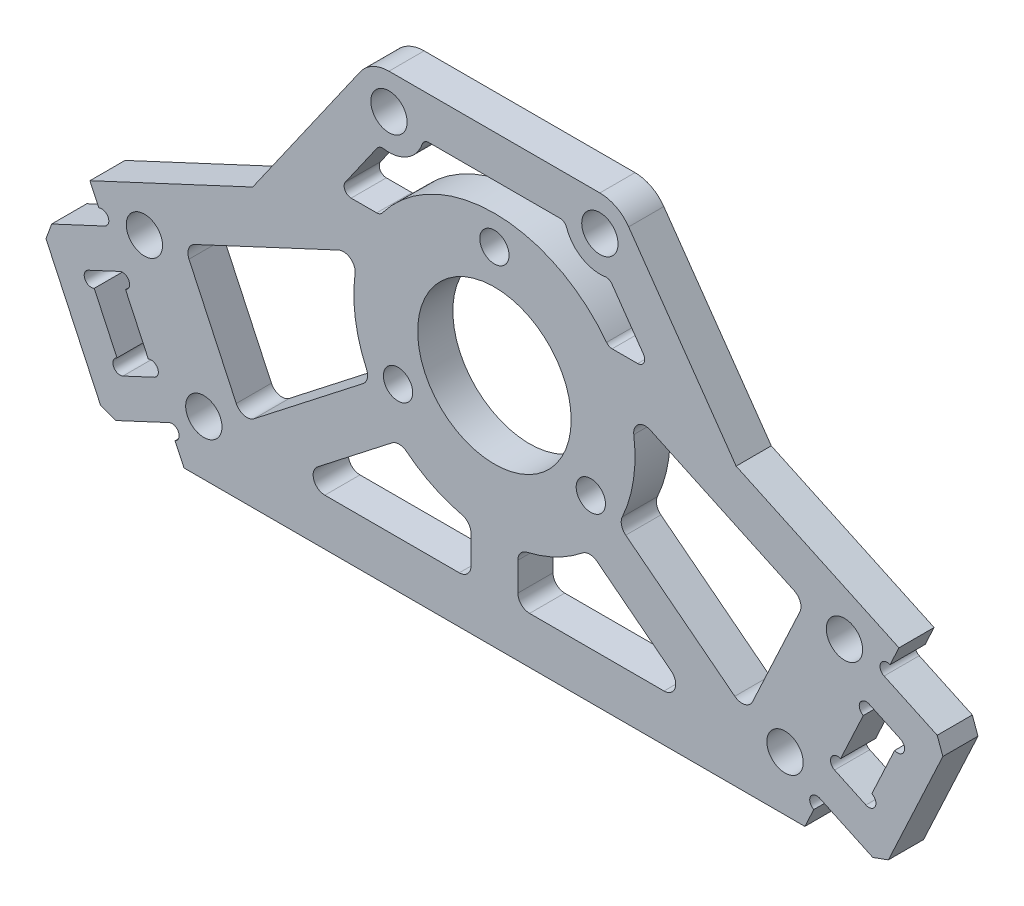
SolidWorks part; units mm, degrees
ref_plane "前视基准面" through (0, 0, 0) normal (0, 0, 1) x (1, 0, 0)
ref_plane "上视基准面" through (0, 0, 0) normal (0, 1, 0) x (1, 0, 0)
ref_plane "右视基准面" through (0, 0, 0) normal (1, 0, 0) x (0, 0, -1)
sketch "草图1" plane through (0, 0, 0) normal (0, 0, 1) x (1, 0, 0)
  line L0 (-34.5264, 8.6099) -> (-26.4967, -8.6099)
  line L1 (-29.455, -2.2658) -> (0, 11.4693) construction
  line L2 (0, -8.6099) -> (0, 8.6099) construction
  line L3 (-34.5264, 8.6099) -> (-5.0714, 22.345)
  line L4 (-26.4967, -8.6099) -> (26.4967, -8.6099)
  line L5 (34.5264, 8.6099) -> (26.4967, -8.6099)
  line L6 (34.5264, 8.6099) -> (5.0714, 22.345)
  circle A0 centre (0, 11.4693) radius 9.5 construction
  circle A1 centre (0, 20.9693) radius 1.25
  circle A2 centre (8.2272, 6.7193) radius 1.25
  circle A3 centre (-8.2272, 6.7193) radius 1.25
  arc A4 (5.0714, 22.345) -> (-5.0714, 22.345) centre (0, 11.4693) ccw
  circle A5 centre (0, 11.4693) radius 6.55
  point P8 (0, 0)
  point P21 (-30.5115, 0)
  dimension "D4" = 19
  dimension "D5" = 2.5
  dimension "D8" = 24
  dimension "D9" = 13.1
  dimension "D1" = 32.5
  dimension "D2" = 25
  dimension "D3" = 19
  dimension "D7" = 2.5
  dimension "D6" = 3
extrude "凸台-拉伸1" add sketch "草图1" along normal mid plane 3
sketch "草图2" plane through (0, 0, 1.5) normal (0, 0, 1) x (1, 0, 0)
  line L0 (-33.2586, 5.891) -> (-38.6964, 3.3553)
  line L1 (-34.5264, 8.6099) -> (-26.4967, -8.6099) construction
  line L2 (-38.6964, 3.3553) -> (-33.2024, -8.4267)
  line L3 (-33.2024, -8.4267) -> (-27.7645, -5.891)
  line L4 (-27.7645, -5.891) -> (-29.0324, -3.1721)
  line L5 (-31.9907, 3.1721) -> (-34.6643, 1.9254)
  line L6 (-34.6643, 1.9254) -> (-31.706, -4.4188)
  line L7 (-31.706, -4.4188) -> (-29.0324, -3.1721)
  line L8 (-31.9907, 3.1721) -> (-33.2586, 5.891)
  line L9 (-30.5115, 0) -> (-33.1852, -1.2467) construction
  line L10 (0, 11.4693) -> (0, -8.6099) construction
  line L11 (-26.4967, -8.6099) -> (26.4967, -8.6099) construction
  line L12 (38.6964, 3.3553) -> (33.2024, -8.4267)
  line L13 (33.2586, 5.891) -> (38.6964, 3.3553)
  line L14 (31.9907, 3.1721) -> (33.2586, 5.891)
  line L15 (31.9907, 3.1721) -> (34.6643, 1.9254)
  line L16 (34.6643, 1.9254) -> (31.706, -4.4188)
  line L17 (31.706, -4.4188) -> (29.0324, -3.1721)
  line L18 (27.7645, -5.891) -> (29.0324, -3.1721)
  line L19 (33.2024, -8.4267) -> (27.7645, -5.891)
  dimension "D1" = 13
  dimension "D2" = 6
  dimension "D3" = 2.95
  dimension "D4" = 7
extrude "凸台-拉伸2" add sketch "草图2" against normal blind 3
sketch "草图3" plane through (0, 0, 1.5) normal (0, 0, 1) x (1, 0, 0)
  line L0 (-34.5264, 8.6099) -> (-33.2586, 5.891) construction
  line L1 (-31.706, -4.4188) -> (-34.6643, 1.9254) construction
  line L3 (-31.9907, 3.1721) -> (-29.0324, -3.1721) construction
  line L4 (-27.7645, -5.891) -> (-26.4967, -8.6099) construction
  line L5 (0, 23.4693) -> (0, -8.6099) construction
  line L6 (-26.4967, -8.6099) -> (26.4967, -8.6099) construction
  circle A0 centre (-33.5121, 6.4348) radius 0.6
  circle A1 centre (-34.4107, 1.3816) radius 0.6
  circle A2 centre (-31.9596, -3.875) radius 0.6
  circle A4 centre (-29.286, -2.6283) radius 0.6
  circle A5 centre (-31.7371, 2.6283) radius 0.6
  circle A6 centre (-27.511, -6.4348) radius 0.6
  arc A7 (5.0714, 22.345) -> (-5.0714, 22.345) centre (0, 11.4693) ccw construction
  circle A8 centre (27.511, -6.4348) radius 0.6
  circle A9 centre (31.7371, 2.6283) radius 0.6
  circle A10 centre (29.286, -2.6283) radius 0.6
  circle A11 centre (31.9596, -3.875) radius 0.6
  circle A12 centre (34.4107, 1.3816) radius 0.6
  circle A13 centre (33.5121, 6.4348) radius 0.6
  dimension "D1" = 1.2
extrude "切除-拉伸1" cut sketch "草图3" against normal through all
sketch "草图4" plane through (0, 0, 1.5) normal (0, 0, 1) x (1, 0, 0)
  line L1 (-5.0714, 22.345) -> (-34.5264, 8.6099) construction
  line L2 (-34.5264, 8.6099) -> (-33.7657, 6.9786) construction
  line L3 (-33.1852, -1.2467) -> (-30.5115, 0) construction
  line L4 (-32.2131, -3.3312) -> (-34.1572, 0.8378) construction
  line L5 (-31.4836, 2.0845) -> (-29.5395, -2.0845) construction
  line L6 (0, 18.0193) -> (0, 4.9193) construction
  circle A0 centre (-29.8752, 6.917) radius 1.55
  circle A4 centre (-24.8038, -3.9587) radius 1.55
  circle A5 centre (0, 11.4693) radius 6.55 construction
  circle A6 centre (24.8038, -3.9587) radius 1.55
  circle A7 centre (29.8752, 6.917) radius 1.55
  dimension "D1" = 3.5
  dimension "D2" = 3.5
  dimension "D3" = 3.1
extrude "切除-拉伸2" cut sketch "草图4" against normal through all
sketch "草图5" plane through (0, 0, 1.5) normal (0, 0, 1) x (1, 0, 0)
  line L4 (-3.3809, 18.7198) -> (-32.8359, 4.9847)
  line L5 (-11.4872, 14.9398) -> (-26.4918, 7.943)
  line L6 (-26.4918, 7.943) -> (-21.5055, -2.7502)
  line L7 (-26.4967, -4.6099) -> (26.4967, -4.6099)
  line L8 (-17.3841, -4.6099) -> (-2, -4.6099)
  line L9 (-2, -4.6099) -> (-2, -0.3628)
  line L10 (-20.6383, -4.6099) -> (0, 11.4693) construction
  line L11 (-17.3841, -4.6099) -> (-8.1046, 2.6197)
  line L12 (-21.5055, -2.7502) -> (-10.5629, 5.7751)
  line L13 (-19.4091, -6.1876) -> (1.2292, 9.8916) construction
  line L14 (-21.8674, -3.0322) -> (-1.2292, 13.047) construction
  line L15 (0, 11.4693) -> (0, -8.6099) construction
  line L16 (-26.4967, -8.6099) -> (26.4967, -8.6099) construction
  line L17 (17.3841, -4.6099) -> (8.1046, 2.6197)
  line L18 (2, -4.6099) -> (2, -0.3628)
  line L19 (17.3841, -4.6099) -> (2, -4.6099)
  line L20 (21.5055, -2.7502) -> (10.5629, 5.7751)
  line L21 (26.4918, 7.943) -> (21.5055, -2.7502)
  line L22 (11.4872, 14.9398) -> (26.4918, 7.943)
  arc A0 (-11.4872, 14.9398) -> (-10.5629, 5.7751) centre (0, 11.4693) ccw
  circle A1 centre (-24.8038, -3.9587) radius 1.55 construction
  arc A2 (-8.1046, 2.6197) -> (-2, -0.3628) centre (0, 11.4693) ccw
  arc A3 (8.1046, 2.6197) -> (2, -0.3628) centre (0, 11.4693) cw
  arc A4 (11.4872, 14.9398) -> (10.5629, 5.7751) centre (0, 11.4693) cw
  dimension "D1" = 24
  dimension "D4" = 3.5
  dimension "D5" = 2
  dimension "D6" = 2
  dimension "D2" = 4
  dimension "D3" = 4
  dimension "D7" = 2
extrude "切除-拉伸3" cut sketch "草图5" against normal through all
fillet "圆角1" radius 1 16 edges at (26.4918, 7.943, 0) (21.5055, -2.7502, 0) (10.5629, 5.7751, 0) (11.4872, 14.9398, 0) (2, -0.3628, 0) (17.3841, -4.6099, 0) (2, -4.6099, 0) (8.1046, 2.6197, 0) (-17.3841, -4.6099, 0) (-2, -0.3628, 0) (-2, -4.6099, 0) (-8.1046, 2.6197, 0) (-10.5629, 5.7751, 0) (-21.5055, -2.7502, 0) (-26.4918, 7.943, 0) (-11.4872, 14.9398, 0)
chamfer "倒角1" distance 1 angle 45 4 edges at (33.2024, -8.4267, 0) (38.6964, 3.3553, 0) (-33.2024, -8.4267, 0) (-38.6964, 3.3553, 0)
sketch "草图6" plane through (0, 0, 1.5) normal (0, 0, 1) x (1, 0, 0)
  line L0 (0, 11.4693) -> (0, 61.4693) construction
  line L1 (-11.4575, 28.1901) -> (-20.6304, 15.0898)
  line L2 (-5.0714, 22.345) -> (-34.5264, 8.6099) construction
  line L3 (-20.6304, 15.0898) -> (-5.0714, 22.345)
  line L4 (-9, 29.4693) -> (9, 29.4693)
  line L5 (20.6304, 15.0898) -> (5.0714, 22.345)
  line L6 (11.4575, 28.1901) -> (20.6304, 15.0898)
  circle A0 centre (-9, 26.4693) radius 1.55
  arc A1 (-9, 29.4693) -> (-11.4575, 28.1901) centre (-9, 26.4693) ccw
  arc A2 (-5.0714, 22.345) -> (5.0714, 22.345) centre (0, 11.4693) cw
  arc A4 (9, 29.4693) -> (11.4575, 28.1901) centre (9, 26.4693) cw
  circle A5 centre (9, 26.4693) radius 1.55
  point P22 (0, 29.4693)
  dimension "D2" = 35
  dimension "D3" = 9
  dimension "D4" = 3.1
  dimension "D5" = 6
  dimension "D6" = 35
  dimension "D1" = 50
extrude "凸台-拉伸3" add sketch "草图6" against normal up to surface (3 mm away)
sketch "草图7" plane through (0, 0, 1.5) normal (0, 0, 1) x (1, 0, 0)
  line L1 (-20.6304, 15.0898) -> (-13.3799, 18.4707) construction
  line L2 (-8.1808, 25.8957) -> (-17.3538, 12.7954)
  line L3 (-9.8032, 23.5788) -> (-13.3799, 18.4707)
  line L4 (-13.3799, 18.4707) -> (-9.7458, 18.4707)
  line L5 (-20.6304, 15.0898) -> (-34.5264, 8.6099) construction
  line L6 (-6.0553, 25.8957) -> (6.0553, 25.8957)
  line L7 (0, 29.4693) -> (0, 11.4693) construction
  line L8 (9, 29.4693) -> (-9, 29.4693) construction
  line L9 (13.3799, 18.4707) -> (9.7458, 18.4707)
  line L10 (9.8032, 23.5788) -> (13.3799, 18.4707)
  arc A0 (9.7458, 18.4707) -> (-9.7458, 18.4707) centre (0, 11.4693) ccw
  arc A1 (-11.8952, 13.052) -> (-10.9126, 6.4778) centre (0, 11.4693) ccw construction
  arc A2 (-9.8032, 23.5788) -> (-6.0553, 25.8957) centre (-9, 26.4693) ccw
  arc A3 (9.8032, 23.5788) -> (6.0553, 25.8957) centre (9, 26.4693) cw
  point P21 (0, 25.8957)
  point P25 (0, 25.8957)
  dimension "D1" = 4
extrude "切除-拉伸4" cut sketch "草图7" against normal through all
fillet "圆角2" radius 0.6 8 edges at (6.0553, 25.8957, 0) (9.8032, 23.5788, 0) (13.3799, 18.4707, 0) (9.7458, 18.4707, 0) (-9.7458, 18.4707, 0) (-9.8032, 23.5788, 0) (-6.0553, 25.8957, 0) (-13.3799, 18.4707, 0)
